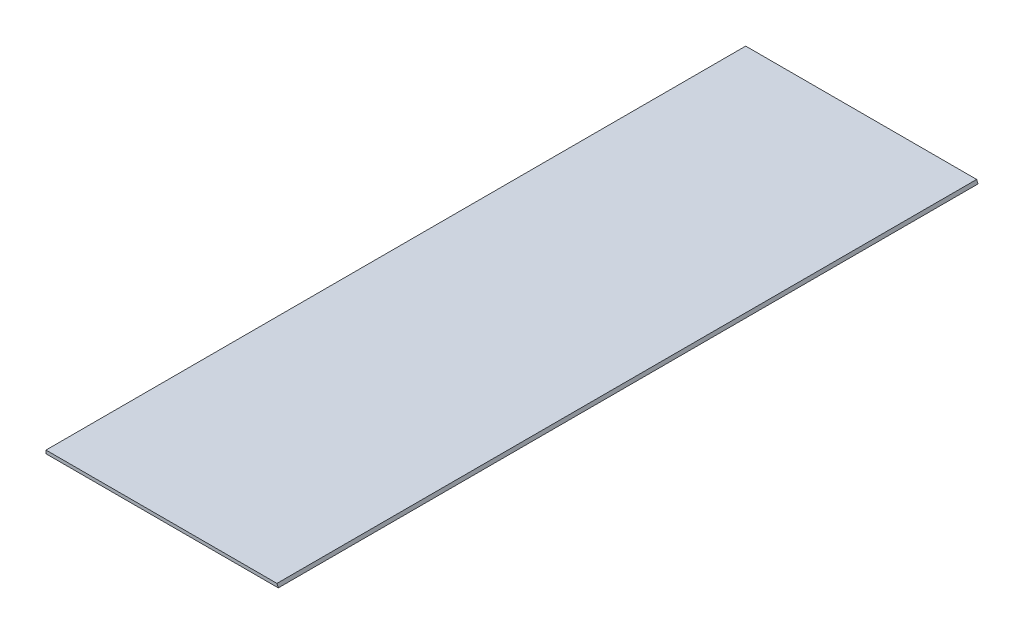
SolidWorks part; units mm, degrees
ref_plane "Front Plane" through (0, 0, 0) normal (0, 0, 1) x (1, 0, 0)
ref_plane "Top Plane" through (0, 0, 0) normal (0, 1, 0) x (1, 0, 0)
ref_plane "Right Plane" through (0, 0, 0) normal (1, 0, 0) x (0, 0, -1)
sketch "Sketch1" plane through (0, 0, 0) normal (0, 0, 1) x (1, 0, 0)
  line L0 (0, 0) -> (0, 2.3622)
  line L1 (0, 2.3622) -> (167.6775, 2.3622)
  line L2 (167.6775, 2.3622) -> (168.656, 0)
  line L3 (168.656, 0) -> (0, 0)
  dimension "D1" = 2.3622
  dimension "D2" = 168.656
  dimension "D3" = 67.5
extrude "Boss-Extrude1" add sketch "Sketch1" along normal blind 508
